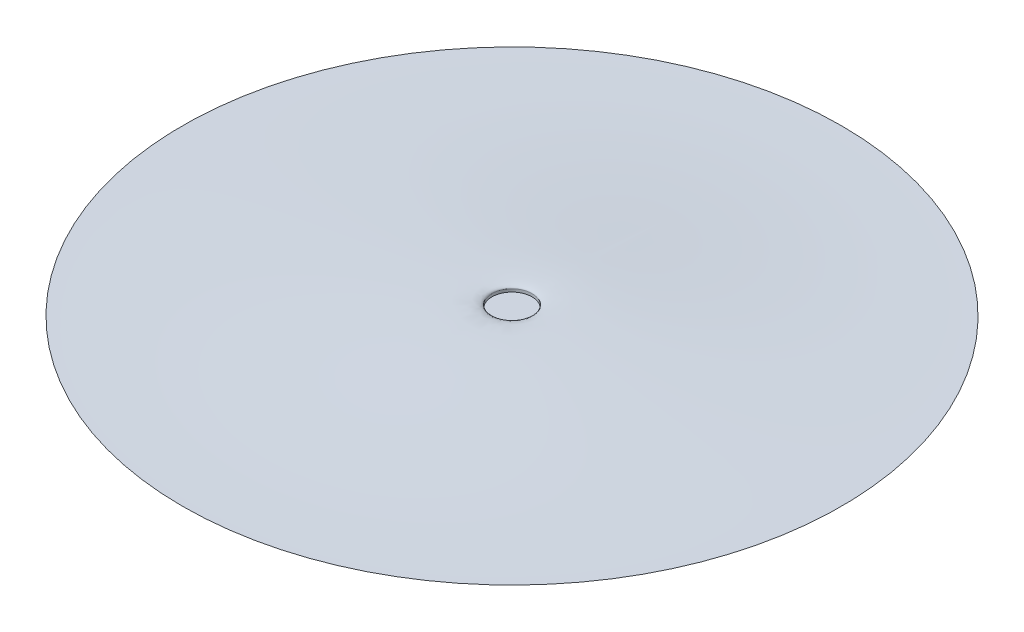
SolidWorks part; units mm, degrees
ref_plane "Front Plane" through (0, 0, 0) normal (0, 0, 1) x (1, 0, 0)
ref_plane "Top Plane" through (0, 0, 0) normal (0, 1, 0) x (1, 0, 0)
ref_plane "Right Plane" through (0, 0, 0) normal (1, 0, 0) x (0, 0, -1)
sketch "Sketch2" plane through (0, 0, 0) normal (1, 0, 0) x (0, 0, -1)
  line L0 (0, 0) -> (127, 0) construction
  line L1 (7.7028, 3.627) -> (7.7028, 2.5437)
  line L2 (0, -2.5437) -> (0, 2.5437)
  line L3 (0, 2.5437) -> (7.7028, 2.5437)
  line L4 (0, -2.5437) -> (7.7028, -2.5437)
  line L7 (7.7028, 3.627) -> (7.7028, 8.1593) construction
  line L8 (7.7028, 8.1593) -> (63.5, 0) construction
  line L9 (63.5, 0) -> (127, 0) construction
  line L10 (7.7028, -4.7397) -> (7.7028, -10.0706) construction
  line L11 (7.7028, -10.0706) -> (63.5, 0) construction
  line L12 (63.5, 0) -> (127, 0) construction
  line L13 (7.7028, 2.5437) -> (7.7028, 0) construction
  line L14 (7.7028, -2.5437) -> (7.7028, -4.7397)
  line L15 (7.7028, 0) -> (7.7028, -2.5437) construction
  spline S0 degree 3 poles (7.7028, 3.627) (7.7028, 8.1593) (63.5, 0) (127, 0) knots 0 0 0 0 1 1 1 1
  spline S1 degree 3 poles (7.7028, -4.7397) (7.7028, -10.0706) (63.5, 0) (127, 0) knots 0 0 0 0 1 1 1 1
  point P6 (14.0909, 0)
  point P9 (0, 0)
  dimension "D1" = 127
revolve "Revolve1" add sketch "Sketch2" angle 360 about L2
